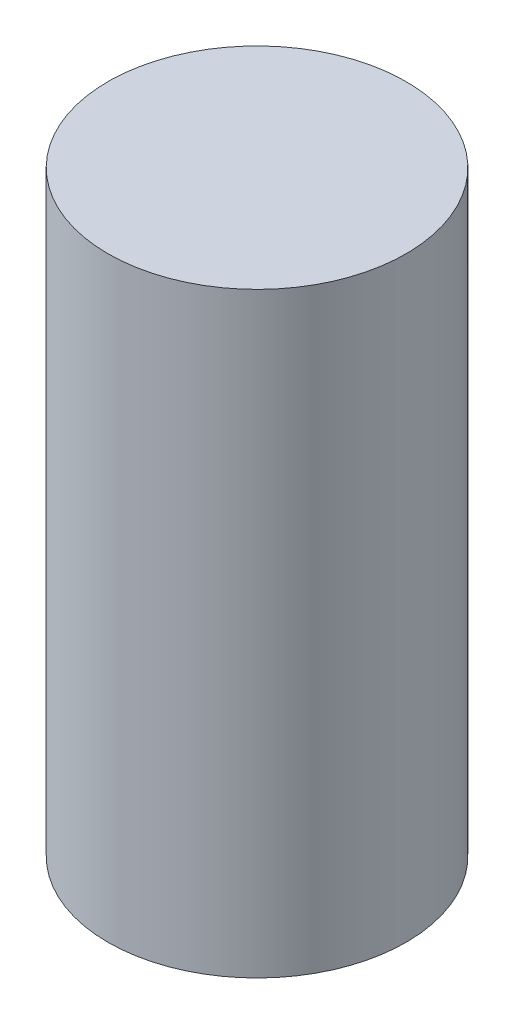
SolidWorks part; units mm, degrees
ref_plane "Alzado" through (0, 0, 0) normal (0, 0, 1) x (1, 0, 0)
ref_plane "Planta" through (0, 0, 0) normal (0, 1, 0) x (1, 0, 0)
ref_plane "Vista lateral" through (0, 0, 0) normal (1, 0, 0) x (0, 0, -1)
sketch "Croquis1" plane through (0, 0, 0) normal (0, 1, 0) x (1, 0, 0)
  circle A0 centre (0, 0) radius 52.5
  dimension "D1" = 105
extrude "Saliente-Extruir1" add sketch "Croquis1" along normal blind 210
sketch "Croquis2" plane through (0, 0, 0) normal (0, -1, 0) x (1, 0, 0)
  circle A0 centre (0, 0) radius 42
  dimension "D1" = 84
extrude "Cortar-Extruir1" cut sketch "Croquis2" against normal blind 196
